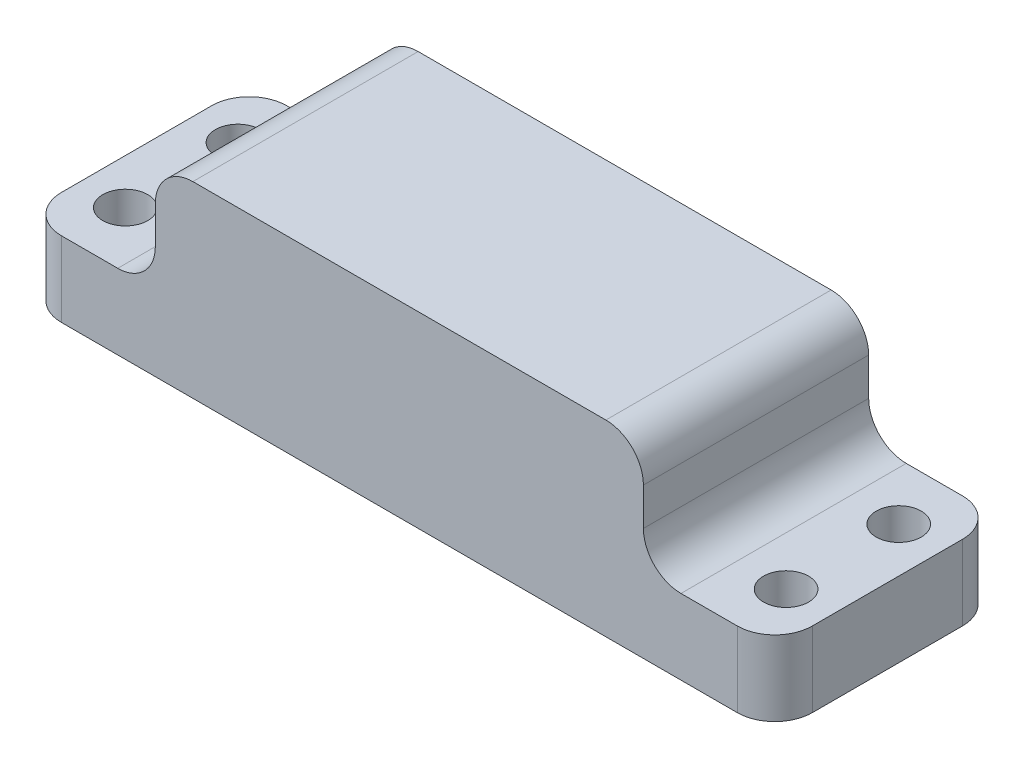
SolidWorks part; units mm, degrees
ref_plane "Front Plane" through (0, 0, 0) normal (0, 0, 1) x (1, 0, 0)
ref_plane "Top Plane" through (0, 0, 0) normal (0, 1, 0) x (1, 0, 0)
ref_plane "Right Plane" through (0, 0, 0) normal (1, 0, 0) x (0, 0, -1)
sketch "Sketch1" plane through (0, 0, 0) normal (0, 0, 1) x (1, 0, 0)
  line L0 (-67.3729, 64.5763) -> (42.6271, 64.5763)
  line L1 (52.6271, 54.5763) -> (52.6271, 44.5763)
  line L2 (62.6271, 34.5763) -> (87.6271, 34.5763)
  line L3 (87.6271, 34.5763) -> (87.6271, 14.5763)
  line L4 (87.6271, 14.5763) -> (-112.3729, 14.5763)
  line L5 (-112.3729, 14.5763) -> (-112.3729, 34.5763)
  line L6 (-112.3729, 34.5763) -> (-87.3729, 34.5763)
  line L7 (-77.3729, 44.5763) -> (-77.3729, 54.5763)
  arc A0 (52.6271, 44.5763) -> (62.6271, 34.5763) centre (62.6271, 44.5763) ccw
  arc A1 (42.6271, 64.5763) -> (52.6271, 54.5763) centre (42.6271, 54.5763) cw
  arc A2 (-67.3729, 64.5763) -> (-77.3729, 54.5763) centre (-67.3729, 54.5763) ccw
  arc A3 (-87.3729, 34.5763) -> (-77.3729, 44.5763) centre (-87.3729, 44.5763) ccw
  point P10 (52.6271, 34.5763)
  point P13 (52.6271, 64.5763)
  point P16 (-77.3729, 64.5763)
  dimension "D5" = 10
  dimension "D1" = 20
  dimension "D2" = 50
  dimension "D3" = 130
  dimension "D4" = 35
extrude "Boss-Extrude1" add sketch "Sketch1" along normal blind 60 contours L0 A1 L1 A0 L2 L3 L4 L5 L6 A3 L7 A2
fillet "Fillet1" radius 10 4 edges at (-112.3729, 24.5763, 0) (-112.3729, 24.5763, 60) (87.6271, 24.5763, 0) (87.6271, 24.5763, 60)
sketch "Sketch5" plane through (0, 34.5763, 0) normal (0, 1, 0) x (1, 0, 0)
  line L0 (-102.3729, -60) -> (-87.3729, -60) construction
  line L1 (-112.3729, -50) -> (-112.3729, -10) construction
  point P0 (-100.3729, -15)
  point P2 (-100.3729, -45)
  point P4 (75.6271, -15)
  point P6 (75.6271, -45)
  point P13 (0, 0)
  point P14 (0, 0)
  point P15 (0, 0)
  point P16 (0, 0)
  dimension "D1" = 176
  dimension "D2" = 30
  dimension "D3" = 15
  dimension "D4" = 12
hole_wizard "CBORE for M5 Hex Head Bolt1" positions "Sketch5" profile "Sketch6" counterbore size "M5" standard "ISO" end condition through all
sketch "Sketch6" plane through (-100.3729, 34.5763, 15) normal (1, 0, 0) x (0, 0, 1)
  line L0 (0, 0) -> (0, 20)
  line L1 (0, 20) -> (4, 20)
  line L3 (4, 20) -> (4, 10)
  line L4 (4, 10) -> (6, 10)
  line L5 (6, 10) -> (6, 0)
  line L7 (6, 0) -> (0, 0)
  line L11 (0, -6.35) -> (0, 107.95) construction
  dimension "Thru Hole Dia." = 8
  dimension "Thru Hole Depth" = 20
  dimension "C'Bore Dia." = 12
  dimension "C'Bore Depth" = 10
